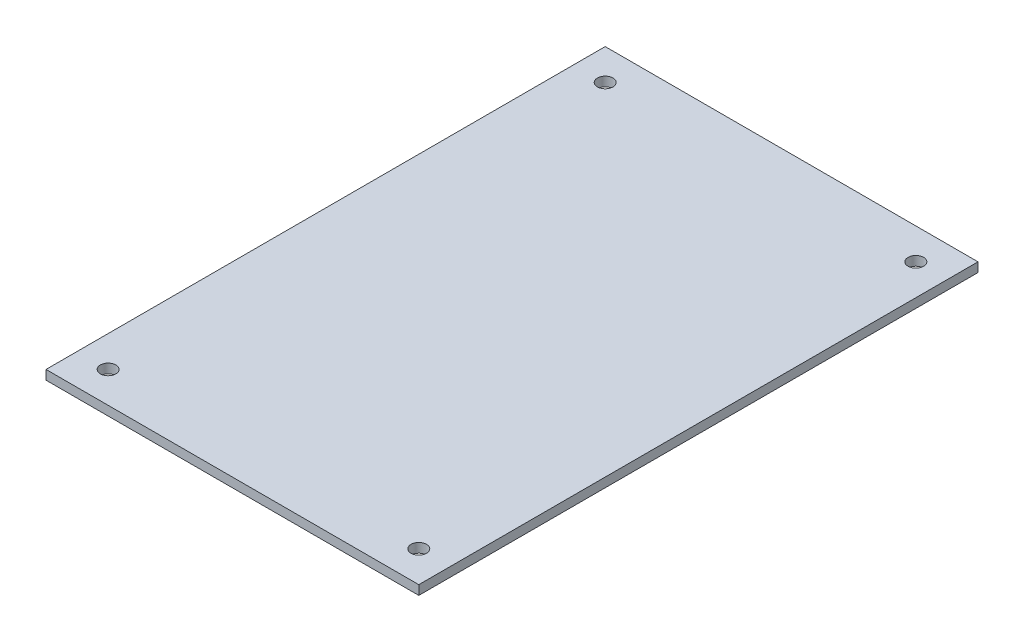
SolidWorks part; units mm, degrees
ref_plane "Front Plane" through (0, 0, 0) normal (0, 0, 1) x (1, 0, 0)
ref_plane "Top Plane" through (0, 0, 0) normal (0, 1, 0) x (1, 0, 0)
ref_plane "Right Plane" through (0, 0, 0) normal (1, 0, 0) x (0, 0, -1)
sketch "Sketch1" plane through (0, 0, 0) normal (0, 1, 0) x (1, 0, 0)
  line L0 (0, 90) -> (0, 0) construction
  line L1 (-60, 90) -> (60, 90)
  line L2 (-60, 90) -> (-60, -90)
  line L3 (-60, -90) -> (60, -90)
  line L4 (60, 90) -> (60, -90)
  line L5 (-60, 90) -> (-53.6704, 80.5056) construction
  line L6 (-60, -90) -> (60, 90) construction
  line L7 (0, 0) -> (-60, 0) construction
  line L8 (-53.6704, 80.5056) -> (0, 0) construction
  line L9 (0, 0) -> (60, -90) construction
  circle A0 centre (-50, 80) radius 2.5
  circle A1 centre (50, 80) radius 2.5
  circle A2 centre (50, -80) radius 2.5
  circle A3 centre (-50, -80) radius 2.5
  point P0 (0, 0)
  point P18 (-60, 90.7505)
  point P19 (-50, 80)
  point P20 (-60, 98.833)
  point P21 (-60, 116.8744)
  dimension "D1" = 10
  dimension "D3" = 5
  dimension "D4" = 160
  dimension "D5" = 100
  dimension "D2" = 10
extrude "Boss-Extrude1" add sketch "Sketch1" along normal blind 3
